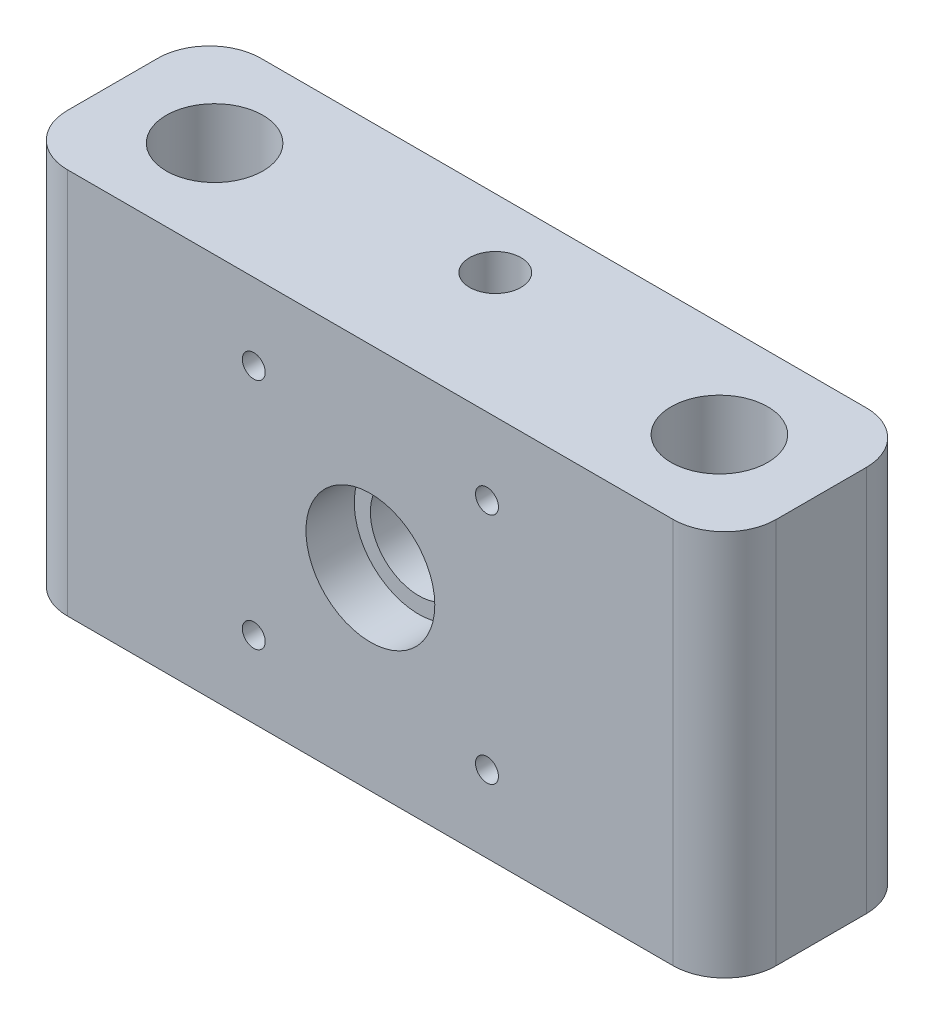
SolidWorks part; units mm, degrees
ref_plane "Front Plane" through (0, 0, 0) normal (0, 0, 1) x (1, 0, 0)
ref_plane "Top Plane" through (0, 0, 0) normal (0, 1, 0) x (1, 0, 0)
ref_plane "Right Plane" through (0, 0, 0) normal (1, 0, 0) x (0, 0, -1)
sketch "Sketch1" plane through (0, 0, 0) normal (0, 0, 1) x (1, 0, 0)
  line L1 (0, 0) -> (69.85, 0)
  line L2 (0, 0) -> (0, 38.1)
  line L3 (0, 38.1) -> (69.85, 38.1)
  line L4 (69.85, 0) -> (69.85, 38.1)
  dimension "D1" = 38.1
  dimension "D2" = 69.85
extrude "Boss-Extrude1" add sketch "Sketch1" along normal mid plane 19.05
sketch "Sketch2" plane through (0, 0, 9.525) normal (0, 0, 1) x (1, 0, 0)
  circle A0 centre (34.925, 19.05) radius 6.35
  dimension "D1" = 12.7
extrude "Cut-Extrude1" cut sketch "Sketch2" against normal blind 4.7625
sketch "Sketch3" plane through (0, 0, 9.525) normal (0, 0, 1) x (1, 0, 0)
  circle A0 centre (34.925, 19.05) radius 4.7625
  dimension "D1" = 9.525
extrude "Cut-Extrude2" cut sketch "Sketch3" against normal through all
sketch "Sketch4" plane through (0, 0, 9.525) normal (0, 0, 1) x (1, 0, 0)
  line L0 (0, 38.1) -> (0, 0) construction
  line L1 (69.85, 38.1) -> (0, 38.1) construction
  line L2 (34.925, 38.1) -> (34.925, 0) construction
  line L3 (0, 0) -> (69.85, 0) construction
  line L4 (0, 19.05) -> (69.85, 19.05) construction
  line L5 (69.85, 0) -> (69.85, 38.1) construction
  circle A0 centre (23.4315, 30.5435) radius 1.1303
  circle A1 centre (46.4185, 30.5435) radius 1.1303
  circle A2 centre (46.4185, 7.5565) radius 1.1303
  circle A3 centre (23.4315, 7.5565) radius 1.1303
  dimension "D1" = 23.4315
  dimension "D2" = 7.5565
  dimension "D3" = 2.2606
extrude "Cut-Extrude3" cut sketch "Sketch4" against normal through all
sketch "Sketch6" plane through (0, 38.1, 0) normal (0, 1, 0) x (1, 0, 0)
  circle A0 centre (10.0451, 0) radius 3.175
  dimension "D1" = 6.35
extrude "Cut-Extrude4" cut sketch "Sketch6" against normal through all
sketch "Sketch7" plane through (0, 38.1, 0) normal (0, 1, 0) x (1, 0, 0)
  circle A0 centre (10.0451, 0) radius 4.7625
  dimension "D1" = 9.525
extrude "Cut-Extrude5" cut sketch "Sketch7" against normal blind 28.575
ref_plane "Plane1" through (34.925, 0, 0) normal (-1, 0, 0) x (0, 0, 1)
mirror "Mirror1" about plane through (34.925, 0, 0) normal (-1, 0, 0) of "Cut-Extrude5", "Cut-Extrude4"
sketch "Sketch8" plane through (0, 38.1, 0) normal (0, 1, 0) x (1, 0, 0)
  line L0 (34.925, 10.4775) -> (34.925, -10.4775) construction
  circle A0 centre (34.925, 2.7886) radius 2.54
  dimension "D1" = 5.08
extrude "Cut-Extrude6" cut sketch "Sketch8" against normal blind 9.652
fillet "Fillet1" radius 5.08 4 edges at (0, 19.05, -9.525) (0, 19.05, 9.525) (69.85, 19.05, 9.525) (69.85, 19.05, -9.525)
